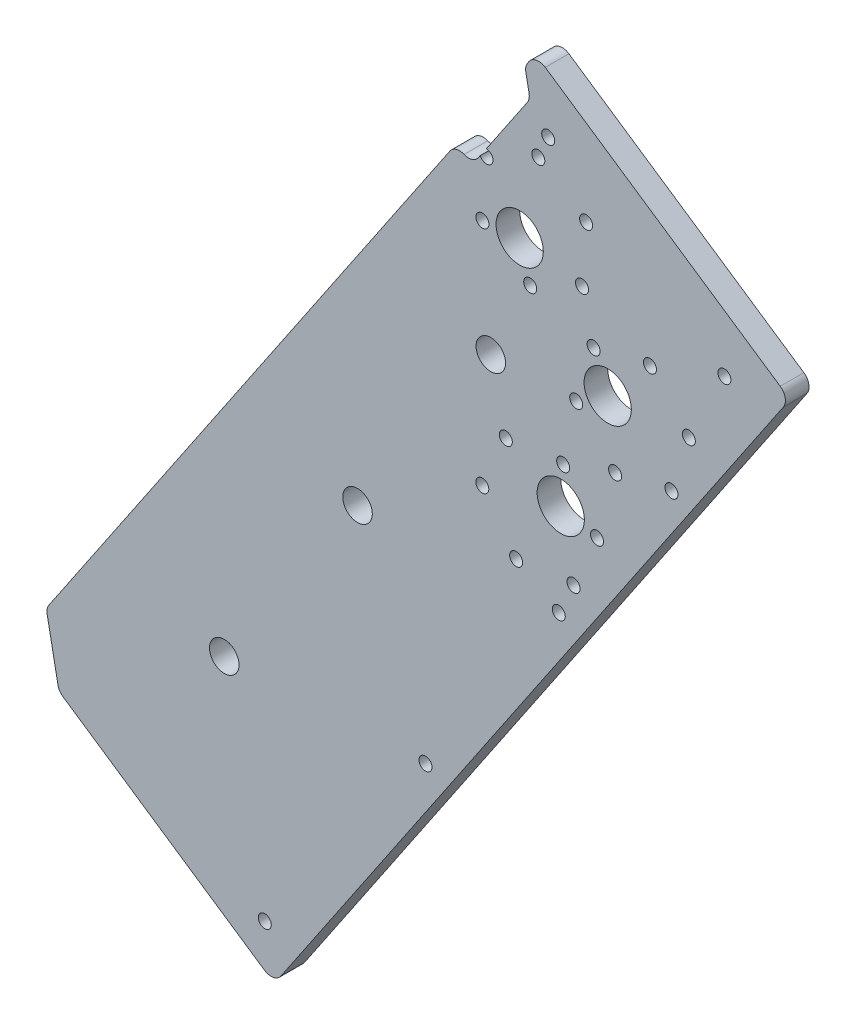
SolidWorks part; units mm, degrees
ref_plane "Front Plane" through (0, 0, 0) normal (0, 0, 1) x (1, 0, 0)
ref_plane "Top Plane" through (0, 0, 0) normal (0, 1, 0) x (1, 0, 0)
ref_plane "Right Plane" through (0, 0, 0) normal (1, 0, 0) x (0, 0, -1)
sketch "Sketch1" plane through (0, 0, 0) normal (0, 0, 1) x (1, 0, 0)
  line L0 (0, 31.75) -> (0, 57.15) construction
  line L1 (31.75, 0) -> (67.31, 0) construction
  line L3 (0, -31.75) -> (0, -97.79) construction
  line L4 (22.4506, -22.4506) -> (58.3717, -58.3717) construction
  line L5 (-22.4506, -22.4506) -> (-72.7401, -72.7401) construction
  line L6 (57.493, 23.8144) -> (29.3332, 12.1502) construction
  line L7 (-40.4112, 40.4112) -> (-22.4506, 22.4506) construction
  line L8 (42.2072, 42.2072) -> (22.4506, 22.4506) construction
  line L9 (71.5729, -29.6465) -> (29.3332, -12.1502) construction
  line L10 (33.5345, -80.9596) -> (12.1502, -29.3332) construction
  line L11 (-37.4226, -90.3462) -> (-12.1502, -29.3332) construction
  circle A0 centre (0, 0) radius 31.75 construction
  circle A3 centre (0, 0) radius 50.8 construction
  dimension "D4" = 63.5
  dimension "D24" = 101.6
  dimension "D2" = 25.4
  dimension "D3" = 35.56
  dimension "D5" = 66.04
  dimension "D6" = 45
  dimension "D7" = 50.8
  dimension "D8" = 71.12
  dimension "D9" = 45
  dimension "D10" = 45
  dimension "D11" = 27.94
  dimension "D12" = 45
  dimension "D13" = 22.5
  dimension "D14" = 22.5
  dimension "D15" = 22.5
  dimension "D16" = 25.4
  dimension "D17" = 45.72
  dimension "D18" = 55.88
  dimension "D19" = 66.04
  dimension "D20" = 22.5
  dimension "D21" = 30.48
sketch "Sketch6" plane through (0, 0, 0) normal (0, 0, 1) x (1, 0, 0)
  line L0 (0, 0) -> (0, 57.15) construction
  line L1 (-68.0069, -76.6709) -> (-109.4868, -48.6565)
  line L2 (-109.4868, -48.6565) -> (-73.9468, 3.9663) construction
  line L3 (-73.9468, 3.9663) -> (-56.6244, -7.7327)
  line L4 (-73.9468, 3.9663) -> (-1.0899, 111.8431)
  line L5 (-1.0899, 111.8431) -> (135.7295, 19.4391)
  line L6 (135.7295, 19.4391) -> (18.4476, -154.2162)
  line L7 (18.4476, -154.2162) -> (-118.3718, -61.8122)
  line L8 (-118.3718, -61.8122) -> (-109.4868, -48.6565)
  arc A0 (0, 57.15) -> (-56.6244, -7.7327) centre (0, 0) ccw
  arc A1 (0, 57.15) -> (70.8293, -29.3385) centre (1.3636, -13.9802) cw
  spline S0 degree 4 poles (72.5802, -14.4204) (72.5732, -14.8939) (72.5509, -15.8408) (72.5026, -17.0238) (72.4142, -18.4418) (72.3202, -19.622) (72.2329, -20.5651) (72.1094, -21.7358) (71.9666, -22.9009) (71.8046, -24.0602) (71.6239, -25.2132) (71.4679, -26.1331) (71.3203, -26.9417) (71.191, -27.6137) (71.0723, -28.2005) (70.9682, -28.6984) (70.8717, -29.1472) (70.8012, -29.4669) (70.7133, -29.8548) (70.619, -30.2629) (70.5011, -30.7621) (70.364, -31.3222) (70.1993, -31.971) (70.0005, -32.7239) (69.7951, -33.4698) (69.582, -34.2143) (69.3614, -34.9567) (69.1333, -35.6968) (68.8388, -36.6189) (68.4706, -37.7207) (68.0195, -38.9988) (67.4748, -40.4488) (66.9013, -41.8877) (66.2993, -43.3149) (65.6691, -44.7298) (65.0111, -46.132) (64.3256, -47.521) (63.613, -48.8963) (62.8736, -50.2574) (62.1078, -51.6038) (61.3159, -52.935) (60.4985, -54.2507) (59.6557, -55.5503) (58.5712, -57.1543) (57.221, -59.0453) (55.576, -61.2004) (53.604, -63.5903) (51.5433, -65.9041) (49.3973, -68.139) (47.1695, -70.2924) (44.8635, -72.3618) (42.4828, -74.3448) (40.0312, -76.2394) (36.8825, -78.4946) (32.9768, -81.016) (28.2508, -83.6809) (21.4155, -86.9191) (14.3083, -89.5267) (6.997, -91.4882) (-0.4519, -92.7974) (-6.6169, -93.4564) (-12.812, -93.702) (-19.0096, -93.5373) (-25.1831, -92.9667) (-31.3064, -91.9964) (-36.5985, -90.8043) (-41.0725, -89.5432) (-44.7523, -88.3359) (-47.6642, -87.2776) (-50.5413, -86.1284) (-53.3811, -84.8896) (-56.1809, -83.563) (-58.5935, -82.3267) (-60.6334, -81.2142) (-62.3138, -80.2525) (-63.6461, -79.4625) (-64.9661, -78.6522) (-66.2736, -77.8217) (-67.4063, -77.0777) (-68.3692, -76.4276) (-69.1659, -75.8779) (-69.7996, -75.4335) (-70.4313, -74.9832) (-71.06, -74.5278) (-71.6725, -74.0775) (-72.2987, -73.6093) (-72.9683, -73.0996) (-73.347, -72.808) (-73.9663, -72.325) (-74.6801, -71.7609) (-75.4046, -71.175) (-76.2838, -70.4507) (-77.1319, -69.735) (-77.9818, -69.0025) (-78.8195, -68.2643) (-79.6511, -67.5155) (-80.4737, -66.7585) (-81.4921, -65.8008) (-82.6974, -64.6343) (-83.8818, -63.4463) (-85.0447, -62.2374) (-85.8084, -61.4205) (-86.1873, -61.0093) (-86.376, -60.8031) knots 0 0 0 0 0 0.008941 0.017882 0.022352 0.026823 0.031293 0.035764 0.044578 0.048985 0.053392 0.057799 0.062207 0.06441 0.066614 0.068817 0.071021 0.072848 0.074676 0.076504 0.078332 0.081987 0.085642 0.089298 0.092953 0.096609 0.100264 0.103919 0.107575 0.114886 0.122197 0.129507 0.136818 0.144129 0.15144 0.158751 0.166062 0.173372 0.180683 0.187994 0.195305 0.202616 0.209927 0.217237 0.231859 0.246481 0.261102 0.275724 0.290346 0.304967 0.319589 0.334211 0.348832 0.363454 0.392697 0.421941 0.451184 0.506141 0.535384 0.564627 0.593871 0.623114 0.652357 0.681601 0.710844 0.740087 0.754709 0.769331 0.783952 0.798574 0.813196 0.827817 0.842439 0.84975 0.857061 0.864371 0.871682 0.878993 0.886304 0.889959 0.893615 0.89727 0.900926 0.904581 0.908237 0.911892 0.915547 0.918186 0.920826 0.926104 0.931382 0.936661 0.941939 0.947217 0.952495 0.957774 0.963052 0.96833 0.978887 0.989443 0.994722 1 1 1 1 1 construction
  spline S1 degree 4 poles (70.8293, -29.3385) (70.8117, -29.4183) (70.776, -29.5781) (70.7133, -29.8548) (70.619, -30.2629) (70.5011, -30.7621) (70.364, -31.3222) (70.1993, -31.971) (70.0005, -32.7239) (69.7951, -33.4698) (69.582, -34.2143) (69.3614, -34.9567) (69.1333, -35.6968) (68.8388, -36.6189) (68.4706, -37.7207) (68.0195, -38.9988) (67.4748, -40.4488) (66.9013, -41.8877) (66.2993, -43.3149) (65.6691, -44.7298) (65.0111, -46.132) (64.3256, -47.521) (63.613, -48.8963) (62.8736, -50.2574) (62.1078, -51.6038) (61.3159, -52.935) (60.4985, -54.2507) (59.6557, -55.5503) (58.5712, -57.1543) (57.221, -59.0453) (55.576, -61.2004) (53.604, -63.5903) (51.5433, -65.9041) (49.3973, -68.139) (47.1695, -70.2924) (44.8635, -72.3618) (42.4828, -74.3448) (40.0312, -76.2394) (36.8825, -78.4946) (32.9768, -81.016) (28.2508, -83.6809) (21.4155, -86.9191) (14.3083, -89.5267) (6.997, -91.4882) (-0.4519, -92.7974) (-6.6169, -93.4564) (-12.812, -93.702) (-19.0096, -93.5373) (-25.1831, -92.9667) (-31.3064, -91.9964) (-36.5985, -90.8043) (-41.0725, -89.5432) (-44.7523, -88.3359) (-47.6642, -87.2776) (-50.5413, -86.1284) (-53.3811, -84.8896) (-56.1809, -83.563) (-58.5935, -82.3267) (-60.6334, -81.2142) (-62.3138, -80.2525) (-63.6461, -79.4625) (-64.9661, -78.6522) (-66.2224, -77.8543) (-67.143, -77.2506) (-67.7363, -76.8537) (-68.0069, -76.6709) knots 0.071021 0.071021 0.071021 0.071021 0.071021 0.072848 0.074676 0.076504 0.078332 0.081987 0.085642 0.089298 0.092953 0.096609 0.100264 0.103919 0.107575 0.114886 0.122197 0.129507 0.136818 0.144129 0.15144 0.158751 0.166062 0.173372 0.180683 0.187994 0.195305 0.202616 0.209927 0.217237 0.231859 0.246481 0.261102 0.275724 0.290346 0.304967 0.319589 0.334211 0.348832 0.363454 0.392697 0.421941 0.451184 0.506141 0.535384 0.564627 0.593871 0.623114 0.652357 0.681601 0.710844 0.740087 0.754709 0.769331 0.783952 0.798574 0.813196 0.827817 0.842439 0.84975 0.857061 0.864371 0.871682 0.878993 0.885158 0.885158 0.885158 0.885158 0.885158
  dimension "D1" = 57.15
  dimension "D2" = 101.6
  dimension "D3" = 63.5
  dimension "D4" = 63.5
  dimension "D5" = 15.875
  dimension "D6" = 101.6
  dimension "D7" = 209.55
extrude "Boss-Extrude2" add sketch "Sketch6" along normal blind 6.35
sketch "Sketch8" plane through (0, 0, 6.35) normal (0, 0, 1) x (1, 0, 0)
  line L0 (-71.0112, -93.7982) -> (-53.3787, -90.3816)
  line L1 (-118.3718, -61.8122) -> (18.4476, -154.2162) construction
  line L2 (-53.3787, -90.3816) -> (-42.8541, -97.4896)
  line L3 (-42.8541, -97.4896) -> (-39.4375, -115.1222)
  line L4 (-39.4375, -115.1222) -> (-71.0112, -93.7982)
  line L5 (18.4476, -154.2162) -> (135.7295, 19.4391) construction
  dimension "D1" = 82.55
  dimension "D2" = 12.7
  dimension "D3" = 12.7
  dimension "D4" = 45
  dimension "D5" = 45
extrude "Cut-Extrude1" cut sketch "Sketch8" against normal through all
sketch "Sketch9" plane through (0, 0, 6.35) normal (0, 0, 1) x (1, 0, 0)
  line L0 (-1.0899, 111.8431) -> (-109.4868, -48.6565)
  line L1 (-1.0899, 111.8431) -> (135.7295, 19.4391)
  line L2 (-109.4868, -48.6565) -> (27.3325, -141.0605)
  line L3 (135.7295, 19.4391) -> (27.3325, -141.0605)
  line L4 (18.4476, -154.2162) -> (135.7295, 19.4391) construction
extrude "Boss-Extrude3" add sketch "Sketch9" against normal through all
sketch "Sketch10" plane through (0, 0, 6.35) normal (0, 0, 1) x (1, 0, 0)
  line L0 (76.6361, 21.2777) -> (4.9965, -84.7966) construction
  line L2 (-39.4375, -115.1222) -> (18.4476, -154.2162) construction
  line L3 (0, 0) -> (-45.2952, -45.2145) construction
  line L4 (-45.2952, -45.2145) -> (4.9965, -84.7966) construction
  line L5 (18.4476, -154.2162) -> (135.7295, 19.4391) construction
  circle A0 centre (4.9965, -84.7966) radius 3.9688
  circle A1 centre (40.8163, -31.7595) radius 3.9687
  circle A2 centre (76.6361, 21.2777) radius 3.9687
  circle A3 centre (-45.2952, -45.2145) radius 3.9687
  dimension "D1" = 7.9375
  dimension "D2" = 50
  dimension "D3" = 50
  dimension "D4" = 128
  dimension "D5" = 64
extrude "Cut-Extrude2" cut sketch "Sketch10" against normal through all
sketch "Sketch11" plane through (0, 0, 6.35) normal (0, 0, 1) x (1, 0, 0)
  circle A0 centre (0, 0) radius 4.5
  dimension "D1" = 9
extrude "Cut-Extrude4" cut sketch "Sketch11" against normal through all contours A0
sketch "Sketch12" plane through (0, 0, 6.35) normal (0, 0, 1) x (1, 0, 0)
  line L0 (135.7295, 19.4391) -> (67.3198, 65.6411)
  line L1 (135.7295, 19.4391) -> (157.0534, 51.0128)
  line L2 (67.3198, 65.6411) -> (88.6438, 97.2148)
  line L3 (157.0534, 51.0128) -> (88.6438, 97.2148)
  line L4 (135.7295, 19.4391) -> (-1.0899, 111.8431) construction
  dimension "D1" = 82.55
  dimension "D2" = 38.1
extrude "Boss-Extrude4" add sketch "Sketch12" against normal through all
sketch "Sketch13" plane through (0, 0, 6.35) normal (0, 0, 1) x (1, 0, 0)
  line L0 (40.8163, -31.7595) -> (76.6361, 21.2777) construction
  line L1 (18.4476, -154.2162) -> (157.0534, 51.0128) construction
  line L2 (58.7262, -5.2409) -> (94.8992, -29.6711) construction
  circle A0 centre (94.8992, -29.6711) radius 1.75
  dimension "D1" = 3.5
  dimension "D2" = 6.35
extrude "Cut-Extrude5" cut sketch "Sketch13" against normal through all
pattern_linear "LPattern1" count 2 spacing 64 along (-0.5597, -0.8287, 0) of "Cut-Extrude5"
sketch "Sketch14" plane through (0, 0, 6.35) normal (0, 0, 1) x (1, 0, 0)
  line L0 (59.0794, -82.7083) -> (94.8992, -29.6711) construction
  line L1 (76.9893, -56.1897) -> (71.727, -52.6357) construction
  line L2 (18.4476, -154.2162) -> (157.0534, 51.0128) construction
  circle A0 centre (71.727, -52.6357) radius 2.54
  dimension "D1" = 5.08
  dimension "D2" = 12.7
sketch "Sketch15" plane through (0, 0, 6.35) normal (0, 0, 1) x (1, 0, 0)
  line L0 (-118.3718, -61.8122) -> (-71.0112, -93.7982) construction
  line L1 (-39.4375, -115.1222) -> (18.4476, -154.2162) construction
  line L2 (18.4476, -154.2162) -> (157.0534, 51.0128) construction
  line L3 (-1.0899, 111.8431) -> (-118.3718, -61.8122) construction
  line L4 (67.3198, 65.6411) -> (-1.0899, 111.8431) construction
  circle A0 centre (-105.1473, -59.2498) radius 1.75
  circle A1 centre (15.8851, -140.9917) radius 1.75
  circle A2 centre (59.0794, -82.7083) radius 1.75 construction
  circle A3 centre (1.4726, 98.6186) radius 1.75
  dimension "D1" = 9.525
  dimension "D2" = 9.525
  dimension "D3" = 9.525
  dimension "D4" = 9.525
  dimension "D5" = 9.525
  dimension "D6" = 9.525
extrude "Cut-Extrude7" cut sketch "Sketch15" against normal through all
sketch "Sketch16" plane through (0, 0, 6.35) normal (0, 0, 1) x (1, 0, 0)
  line L0 (157.0534, 51.0128) -> (88.6438, 97.2148) construction
  line L1 (88.6438, 97.2148) -> (67.3198, 65.6411) construction
  line L2 (18.4476, -154.2162) -> (157.0534, 51.0128) construction
  circle A0 centre (92.0604, 79.5822) radius 1.75
  circle A1 centre (139.4209, 47.5962) radius 1.75
  circle A2 centre (94.8992, -29.6711) radius 1.75 construction
  dimension "D1" = 12.7
  dimension "D2" = 12.7
  dimension "D3" = 12.7
  dimension "D4" = 12.7
extrude "Cut-Extrude8" cut sketch "Sketch16" against normal through all
sketch "Sketch17" plane through (0, 0, 6.35) normal (0, 0, 1) x (1, 0, 0)
  line L0 (0, 0) -> (-26.3114, 17.77) construction
  line L1 (0, 0) -> (17.77, 26.3114) construction
  line L2 (18.4476, -154.2162) -> (157.0534, 51.0128) construction
  circle A0 centre (-26.3114, 17.77) radius 1.75
  circle A1 centre (17.77, 26.3114) radius 1.75
  circle A2 centre (94.8992, -29.6711) radius 1.75 construction
  dimension "D1" = 31.75
extrude "Cut-Extrude9" cut sketch "Sketch17" against normal through all
sketch "Sketch18" plane through (0, 0, 6.35) normal (0, 0, 1) x (1, 0, 0)
  line L0 (76.6361, 21.2777) -> (108.0518, 27.3649) construction
  line L1 (157.0534, 51.0128) -> (88.6438, 97.2148) construction
  line L2 (76.6361, 21.2777) -> (84.396, 52.3226) construction
  line L3 (76.6361, 21.2777) -> (95.4299, -4.622) construction
  line L4 (95.4299, -4.622) -> (89.7643, -8.7331) construction
  line L5 (108.0518, 27.3649) -> (114.7254, 25.2525) construction
  line L6 (84.396, 52.3226) -> (88.3138, 58.1235) construction
  line L7 (88.6438, 97.2148) -> (67.3198, 65.6411) construction
  line L10 (89.7643, -8.7331) -> (114.7254, 25.2525) construction
  line L11 (114.7254, 25.2525) -> (88.3138, 58.1235) construction
  line L13 (87.2234, 42.6619) -> (101.1588, 49.4484) construction
  line L14 (101.1588, 49.4484) -> (102.2492, 64.91) construction
  line L15 (102.2492, 64.91) -> (89.4042, 73.5851) construction
  line L16 (89.4042, 73.5851) -> (75.4689, 66.7986) construction
  line L17 (75.4689, 66.7986) -> (74.3785, 51.337) construction
  line L18 (74.3785, 51.337) -> (87.2234, 42.6619) construction
  line L19 (99.5891, 21.9147) -> (110.0478, 10.4751) construction
  line L20 (110.0478, 10.4751) -> (125.1842, 13.8128) construction
  line L21 (125.1842, 13.8128) -> (129.8618, 28.5902) construction
  line L22 (129.8618, 28.5902) -> (119.4031, 40.0298) construction
  line L23 (119.4031, 40.0298) -> (104.2667, 36.6921) construction
  line L24 (104.2667, 36.6921) -> (99.5891, 21.9147) construction
  line L25 (105.1804, -7.1221) -> (96.0772, 5.4231) construction
  line L26 (96.0772, 5.4231) -> (80.6611, 3.812) construction
  line L27 (80.6611, 3.812) -> (74.3483, -10.3442) construction
  line L28 (74.3483, -10.3442) -> (83.4515, -22.8894) construction
  line L29 (83.4515, -22.8894) -> (98.8676, -21.2783) construction
  line L30 (98.8676, -21.2783) -> (105.1804, -7.1221) construction
  circle A0 centre (114.7254, 25.2525) radius 18.5 construction
  circle A1 centre (88.3138, 58.1235) radius 18.5 construction
  circle A2 centre (89.7643, -8.7331) radius 18.5 construction
  circle A3 centre (88.3138, 58.1235) radius 13.4234 construction
  circle A4 centre (114.7254, 25.2525) radius 13.4234 construction
  circle A5 centre (89.7643, -8.7331) radius 13.4234 construction
  circle A6 centre (75.4689, 66.7986) radius 1.75
  circle A7 centre (74.3785, 51.337) radius 1.75
  circle A8 centre (87.2234, 42.6619) radius 1.75
  circle A9 centre (101.1588, 49.4484) radius 1.75
  circle A10 centre (102.2492, 64.91) radius 1.75
  circle A11 centre (89.4042, 73.5851) radius 1.75
  circle A12 centre (99.5891, 21.9147) radius 1.75
  circle A13 centre (104.2667, 36.6921) radius 1.75
  circle A14 centre (119.4031, 40.0298) radius 1.75
  circle A15 centre (129.8618, 28.5902) radius 1.75
  circle A16 centre (125.1842, 13.8128) radius 1.75
  circle A17 centre (110.0478, 10.4751) radius 1.75
  circle A18 centre (105.1804, -7.1221) radius 1.75
  circle A19 centre (96.0772, 5.4231) radius 1.75
  circle A20 centre (80.6611, 3.812) radius 1.75
  circle A21 centre (74.3483, -10.3442) radius 1.75
  circle A22 centre (83.4515, -22.8894) radius 1.75
  circle A23 centre (98.8676, -21.2783) radius 1.75
  circle A24 centre (84.396, 52.3226) radius 6.35
  circle A25 centre (108.0518, 27.3649) radius 6.35
  circle A26 centre (95.4299, -4.622) radius 6.35
  dimension "D6" = 37
  dimension "D8" = 3.5
  dimension "D9" = 12.7
  dimension "D1" = 45
  dimension "D2" = 65
  dimension "D3" = 65
  dimension "D4" = 32
  dimension "D5" = 7
  dimension "D7" = 31
extrude "Cut-Extrude10" cut sketch "Sketch18" against normal through all
sketch "Sketch19" plane through (0, 0, 6.35) normal (0, 0, 1) x (1, 0, 0)
  line L0 (67.3198, 65.6411) -> (-1.0899, 111.8431)
  line L1 (67.3198, 65.6411) -> (-50.4056, -108.6709)
  line L2 (-1.0899, 111.8431) -> (-118.8153, -62.4689)
  line L3 (-50.4056, -108.6709) -> (-118.8153, -62.4689)
extrude "Cut-Extrude11" cut sketch "Sketch19" against normal through all
sketch "Sketch20" plane through (0, 0, 6.35) normal (0, 0, 1) x (1, 0, 0)
  line L0 (85.8006, 93.0049) -> (87.1672, 85.9519)
  line L1 (88.6438, 97.2148) -> (-42.8541, -97.4896) construction
  line L2 (87.1672, 85.9519) -> (71.5296, 62.7979)
  line L3 (71.5296, 62.7979) -> (67.3198, 65.6411)
  line L4 (67.3198, 65.6411) -> (85.8006, 93.0049)
  dimension "D1" = 45
  dimension "D2" = 90
  dimension "D3" = 5.08
  dimension "D4" = 5.08
  dimension "D5" = 38.1
extrude "Cut-Extrude12" cut sketch "Sketch20" against normal through all
fillet "Fillet1" radius 3.175 8 edges at (71.5296, 62.7979, 3.175) (18.4476, -154.2162, 3.175) (-39.4375, -115.1222, 3.175) (-42.8541, -97.4896, 3.175) (157.0534, 51.0128, 3.175) (88.6438, 97.2148, 3.175) (85.8006, 93.0049, 3.175) (87.1672, 85.9519, 3.175)
fillet "Fillet2" radius 3.175 1 edges at (67.3198, 65.6411, 3.175)
